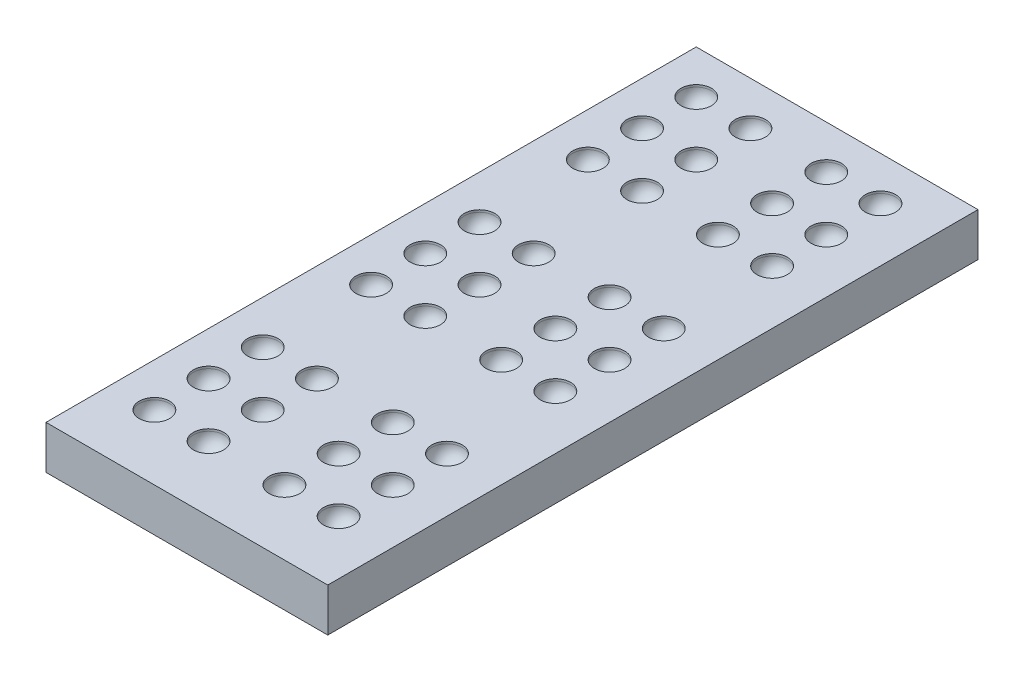
SolidWorks part; units mm, degrees
ref_plane "Front Plane" through (0, 0, 0) normal (0, 0, 1) x (1, 0, 0)
ref_plane "Top Plane" through (0, 0, 0) normal (0, 1, 0) x (1, 0, 0)
ref_plane "Right Plane" through (0, 0, 0) normal (1, 0, 0) x (0, 0, -1)
sketch "Sketch1" plane through (0, 0, 0) normal (0, 1, 0) x (1, 0, 0)
  line L1 (0, 0) -> (13, 0)
  line L2 (0, 0) -> (0, 30)
  line L3 (0, 30) -> (13, 30)
  line L4 (13, 0) -> (13, 30)
  dimension "D1" = 13
  dimension "D2" = 30
extrude "Boss-Extrude1" add sketch "Sketch1" along normal blind 2
sketch "Sketch2" plane through (0, 2, 0) normal (0, 1, 0) x (1, 0, 0)
  line L0 (2, 28) -> (4.5, 28) construction
  line L1 (2, 28) -> (2, 25.5) construction
  line L2 (0, 30) -> (0, 0) construction
  line L3 (13, 30) -> (0, 30) construction
  circle A0 centre (2, 28) radius 0.7
  circle A1 centre (4.5, 28) radius 0.7
  circle A2 centre (4.5, 25.5) radius 0.7
  circle A3 centre (4.5, 23) radius 0.7
  circle A4 centre (2, 25.5) radius 0.7
  circle A5 centre (2, 23) radius 0.7
  dimension "D1" = 1.4
  dimension "D7" = 2
  dimension "D8" = 2
  dimension "D4" = 90
  dimension "D5" = 2.5
  dimension "D6" = 2.5
  dimension "D2" = 2
  dimension "D3" = 3
extrude "Cut-Extrude1" cut sketch "Sketch2" against normal blind 0.1
sketch "Sketch3" plane through (0, 1.9, 0) normal (0, 1, 0) x (1, 0, 0)
  line L0 (2, 28.7) -> (2, 12.1923) construction
  line L1 (2, 28.7) -> (2, 27.3)
  circle A1 centre (2, 28) radius 0.7
  arc A2 (2, 28.7) -> (2, 27.3) centre (2, 28) ccw
  dimension "D1" = 0
revolve "Cut-Revolve1" cut sketch "Sketch3" angle 360 about L0
pattern_linear "LPattern1" count 2 spacing 2.5 along (1, 0, 0) count 3 spacing 2.5 along (0, 0, 1) of "Cut-Revolve1"
pattern_linear "LPattern3" count 2 spacing 6 along (1, 0, 0) count 3 spacing 10 along (0, 0, 1) of "Cut-Extrude1", "Cut-Revolve1", "LPattern1"
